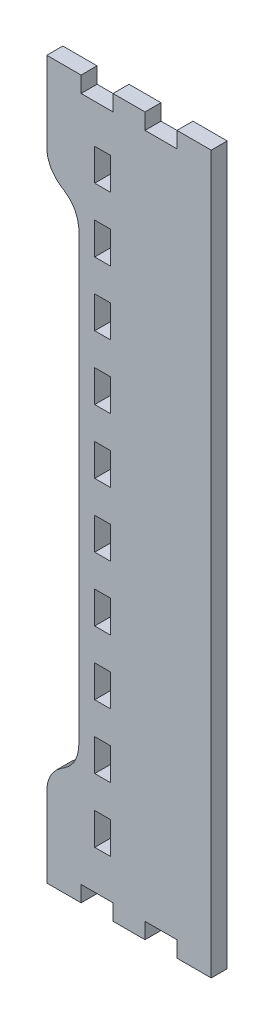
SolidWorks part; units mm, degrees
ref_plane "Front Plane" through (0, 0, 0) normal (0, 0, 1) x (1, 0, 0)
ref_plane "Top Plane" through (0, 0, 0) normal (0, 1, 0) x (1, 0, 0)
ref_plane "Right Plane" through (0, 0, 0) normal (1, 0, 0) x (0, 0, -1)
sketch "Model" plane through (0, 0, 0) normal (0, 0, 1) x (1, 0, 0)
  line L534 (863.2622, 23.2006) -> (875.5278, 23.2006)
  line L535 (875.5278, 23.2006) -> (875.5278, 28.9154)
  line L536 (875.5278, 28.9154) -> (886.9578, 28.9154)
  line L537 (886.9578, 28.9154) -> (886.9578, 23.2006)
  line L538 (886.9578, 23.2006) -> (898.3878, 23.2006)
  line L539 (898.3878, 23.2006) -> (898.3878, 28.9154)
  line L540 (898.3878, 28.9154) -> (909.8178, 28.9154)
  line L541 (909.8178, 28.9154) -> (909.8178, 23.2006)
  line L542 (909.8178, 23.2006) -> (922.081, 23.2006)
  line L543 (922.081, 23.2006) -> (922.081, 279.6311)
  line L544 (922.081, 279.6311) -> (909.8178, 279.6311)
  line L545 (909.8178, 279.6311) -> (909.8178, 273.9161)
  line L546 (909.8178, 273.9161) -> (898.3878, 273.9161)
  line L547 (898.3878, 273.9161) -> (898.3878, 279.6311)
  line L548 (898.3878, 279.6311) -> (886.9578, 279.6311)
  line L549 (886.9578, 279.6311) -> (886.9578, 273.9161)
  line L550 (886.9578, 273.9161) -> (875.5278, 273.9161)
  line L551 (875.5278, 273.9161) -> (875.5278, 279.6311)
  line L552 (875.5278, 279.6311) -> (863.2622, 279.6311)
  line L553 (863.2622, 279.6311) -> (863.2622, 251.0551)
  line L554 (863.2622, 251.0551) -> (863.2622, 250.3167)
  line L555 (863.2622, 250.3167) -> (863.6483, 248.0981)
  line L556 (863.6483, 248.0981) -> (864.5423, 245.776)
  line L557 (864.5423, 245.776) -> (864.7913, 245.3404)
  line L558 (864.7913, 245.3404) -> (865.0427, 244.9065)
  line L559 (865.0427, 244.9065) -> (866.6099, 242.9744)
  line L560 (866.6099, 242.9744) -> (868.5428, 241.4077)
  line L561 (868.5428, 241.4077) -> (868.9772, 241.1567)
  line L562 (868.9772, 241.1567) -> (869.409, 240.906)
  line L563 (869.409, 240.906) -> (871.3445, 239.3404)
  line L564 (871.3445, 239.3404) -> (872.9091, 237.4085)
  line L565 (872.9091, 237.4085) -> (873.1606, 236.9729)
  line L566 (873.1606, 236.9729) -> (873.412, 236.539)
  line L567 (873.412, 236.539) -> (874.3036, 234.217)
  line L568 (874.3036, 234.217) -> (874.6947, 231.9983)
  line L569 (874.6947, 231.9983) -> (874.6947, 231.2581)
  line L570 (874.6947, 231.2581) -> (874.6947, 71.5726)
  line L571 (874.6947, 71.5726) -> (874.6922, 71.071)
  line L572 (874.6922, 71.071) -> (874.3036, 68.6153)
  line L573 (874.3036, 68.6153) -> (873.412, 66.2932)
  line L574 (873.412, 66.2932) -> (873.1606, 65.8579)
  line L575 (873.1606, 65.8579) -> (872.9091, 65.4238)
  line L576 (872.9091, 65.4238) -> (871.3445, 63.4919)
  line L577 (871.3445, 63.4919) -> (869.409, 61.9249)
  line L578 (869.409, 61.9249) -> (868.9772, 61.674)
  line L579 (868.9772, 61.674) -> (868.5428, 61.4233)
  line L580 (868.5428, 61.4233) -> (866.6099, 59.8579)
  line L581 (866.6099, 59.8579) -> (865.0427, 57.9257)
  line L582 (865.0427, 57.9257) -> (864.7913, 57.4904)
  line L583 (864.7913, 57.4904) -> (864.5423, 57.0563)
  line L584 (864.5423, 57.0563) -> (863.6483, 54.7342)
  line L585 (863.6483, 54.7342) -> (863.2622, 52.5155)
  line L586 (863.2622, 52.5155) -> (863.2622, 51.7759)
  line L587 (863.2622, 51.7759) -> (863.2622, 23.2006)
  line L588 (880.4072, 254.2845) -> (880.4072, 259.9995)
  line L589 (880.4072, 259.9995) -> (886.1222, 259.9995)
  line L590 (886.1222, 259.9995) -> (886.1222, 248.5705)
  line L591 (886.1222, 248.5705) -> (880.4072, 248.5705)
  line L592 (880.4072, 248.5705) -> (880.4072, 254.2845)
  line L593 (880.4072, 231.425) -> (880.4072, 237.141)
  line L594 (880.4072, 237.141) -> (886.1222, 237.141)
  line L595 (886.1222, 237.141) -> (886.1222, 225.7105)
  line L596 (886.1222, 225.7105) -> (880.4072, 225.7105)
  line L597 (880.4072, 225.7105) -> (880.4072, 231.425)
  line L598 (880.4072, 208.566) -> (880.4072, 214.2807)
  line L599 (880.4072, 214.2807) -> (886.1222, 214.2807)
  line L600 (886.1222, 214.2807) -> (886.1222, 202.85)
  line L601 (886.1222, 202.85) -> (880.4072, 202.85)
  line L602 (880.4072, 202.85) -> (880.4072, 208.566)
  line L603 (880.4072, 185.7057) -> (880.4072, 191.4205)
  line L604 (880.4072, 191.4205) -> (886.1222, 191.4205)
  line L605 (886.1222, 191.4205) -> (886.1222, 179.991)
  line L606 (886.1222, 179.991) -> (880.4072, 179.991)
  line L607 (880.4072, 179.991) -> (880.4072, 185.7057)
  line L608 (880.4072, 162.8455) -> (880.4072, 168.5605)
  line L609 (880.4072, 168.5605) -> (886.1222, 168.5605)
  line L610 (886.1222, 168.5605) -> (886.1222, 157.1308)
  line L611 (886.1222, 157.1308) -> (880.4072, 157.1308)
  line L612 (880.4072, 157.1308) -> (880.4072, 162.8455)
  line L613 (880.4072, 139.9855) -> (880.4072, 145.7)
  line L614 (880.4072, 145.7) -> (886.1222, 145.7)
  line L615 (886.1222, 145.7) -> (886.1222, 134.2705)
  line L616 (886.1222, 134.2705) -> (880.4072, 134.2705)
  line L617 (880.4072, 134.2705) -> (880.4072, 139.9855)
  line L618 (880.4072, 117.125) -> (880.4072, 122.841)
  line L619 (880.4072, 122.841) -> (886.1222, 122.841)
  line L620 (886.1222, 122.841) -> (886.1222, 111.4105)
  line L621 (886.1222, 111.4105) -> (880.4072, 111.4105)
  line L622 (880.4072, 111.4105) -> (880.4072, 117.125)
  line L623 (880.4072, 94.266) -> (880.4072, 99.9807)
  line L624 (880.4072, 99.9807) -> (886.1222, 99.9807)
  line L625 (886.1222, 99.9807) -> (886.1222, 88.55)
  line L626 (886.1222, 88.55) -> (880.4072, 88.55)
  line L627 (880.4072, 88.55) -> (880.4072, 94.266)
  line L628 (880.4072, 71.4057) -> (880.4072, 77.1205)
  line L629 (880.4072, 77.1205) -> (886.1222, 77.1205)
  line L630 (886.1222, 77.1205) -> (886.1222, 65.691)
  line L631 (886.1222, 65.691) -> (880.4072, 65.691)
  line L632 (880.4072, 65.691) -> (880.4072, 71.4057)
  line L633 (880.4072, 48.5455) -> (880.4072, 54.2605)
  line L634 (880.4072, 54.2605) -> (886.1222, 54.2605)
  line L635 (886.1222, 54.2605) -> (886.1222, 42.8308)
  line L636 (886.1222, 42.8308) -> (880.4072, 42.8308)
  line L637 (880.4072, 42.8308) -> (880.4072, 48.5455)
extrude "Boss-Extrude1" add sketch "Model" along normal blind 5.715
